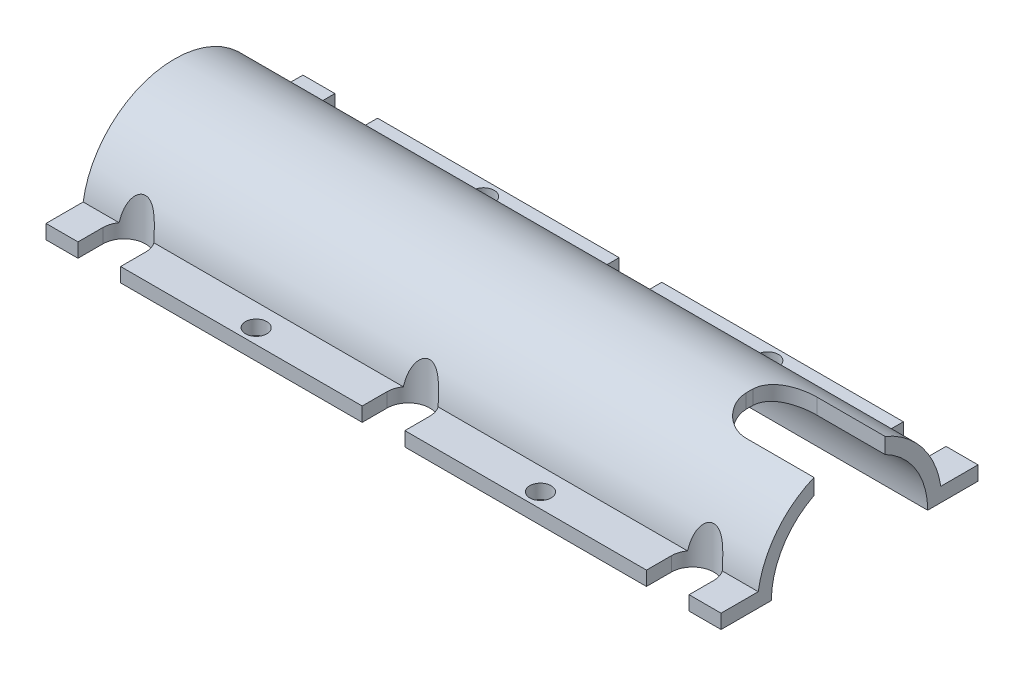
SolidWorks part; units mm, degrees
ref_plane "Спереди" through (0, 0, 0) normal (0, 0, 1) x (1, 0, 0)
ref_plane "Сверху" through (0, 0, 0) normal (0, 1, 0) x (1, 0, 0)
ref_plane "Справа" through (0, 0, 0) normal (1, 0, 0) x (0, 0, -1)
sketch "Эскиз1" plane through (0, 0, 0) normal (1, 0, 0) x (0, 0, -1)
  line L0 (11, 0) -> (18.0795, 0)
  line L1 (18.0795, 0) -> (18.0795, 2)
  line L2 (18.0795, 2) -> (12.8481, 2)
  line L3 (0, 0) -> (0, 11) construction
  line L4 (-18.0795, 2) -> (-12.848, 2.0004)
  line L5 (-18.0795, 0) -> (-18.0795, 2)
  line L6 (-11, 0) -> (-18.0795, 0)
  arc A0 (-11, 0) -> (11, 0) centre (0, 0) cw
  arc A4 (-12.848, 2.0004) -> (12.8481, 2) centre (0, 0) cw
  dimension "D1" = 2
  dimension "D2" = 13.0028
extrude "Бобышка-Вытянуть1" add sketch "Эскиз1" along normal blind 95
sketch "Эскиз2" plane through (0, 2.0015, 0.0002) normal (0, 1, 0.0001) x (1, 0, 0)
  line L0 (0, -18.0793) -> (0, -14.5793) construction
  line L1 (4.5, -14.5793) -> (4.5, -18.2988)
  line L2 (0, -12.8479) -> (0, -18.0793) construction
  line L5 (0, -14.5793) -> (7.5, -14.5793) construction
  line L6 (4.5, -18.2988) -> (10.5, -18.2988)
  line L32 (10.5, -18.2988) -> (10.5, -14.5793)
  line L33 (50.5, -18.2988) -> (50.5, -14.5793)
  line L34 (44.5, -14.5793) -> (44.5, -18.2988)
  line L35 (44.5, -18.2988) -> (50.5, -18.2988)
  line L36 (90.5, -18.2988) -> (90.5, -14.5793)
  line L37 (84.5, -14.5793) -> (84.5, -18.2988)
  line L38 (84.5, -18.2988) -> (90.5, -18.2988)
  line L39 (84.5, 18.2988) -> (90.5, 18.2988)
  line L40 (84.5, 14.5793) -> (84.5, 18.2988)
  line L41 (90.5, 18.2988) -> (90.5, 14.5793)
  line L42 (44.5, 18.2988) -> (50.5, 18.2988)
  line L43 (44.5, 14.5793) -> (44.5, 18.2988)
  line L44 (50.5, 18.2988) -> (50.5, 14.5793)
  line L45 (4.5, 18.2988) -> (10.5, 18.2988)
  line L46 (4.5, 14.5793) -> (4.5, 18.2988)
  line L47 (10.5, 18.2988) -> (10.5, 14.5793)
  circle A0 centre (27.5, -16) radius 1.5
  circle A1 centre (67.5, -16) radius 1.5
  circle A2 centre (67.5, 16) radius 1.5
  circle A3 centre (27.5, 16) radius 1.5
  arc A10 (10.5, -14.5793) -> (4.5, -14.5793) centre (7.5, -14.5793) ccw
  arc A11 (50.5, -14.5793) -> (44.5, -14.5793) centre (47.5, -14.5793) ccw
  arc A12 (90.5, -14.5793) -> (84.5, -14.5793) centre (87.5, -14.5793) ccw
  arc A13 (90.5, 14.5793) -> (84.5, 14.5793) centre (87.5, 14.5793) cw
  arc A14 (50.5, 14.5793) -> (44.5, 14.5793) centre (47.5, 14.5793) cw
  arc A15 (10.5, 14.5793) -> (4.5, 14.5793) centre (7.5, 14.5793) cw
  dimension "D1" = 2
  dimension "D2" = 3
extrude "Вырез-Вытянуть1" cut sketch "Эскиз2" against normal through all and the other way through all
sketch "Эскиз3" plane through (0, 0, 0) normal (0, -1, 0) x (1, 0, 0)
  line L0 (0, 0) -> (95, 0) construction
  line L1 (95, -11) -> (95, 11) construction
  line L3 (85.4096, 5) -> (95, 5)
  line L4 (80.9096, 0.5) -> (80.9096, -0.5)
  line L5 (85.4096, -5) -> (95, -5)
  line L6 (95, 5) -> (95, -5)
  line L7 (80.9096, 5) -> (95, -5) construction
  line L8 (80.9096, -5) -> (95, 5) construction
  arc A0 (80.9096, 0.5) -> (85.4096, 5) centre (85.4096, 0.5) cw
  arc A1 (80.9096, -0.5) -> (85.4096, -5) centre (85.4096, -0.5) ccw
  point P5 (87.9548, 0)
  dimension "D1" = 4.5
  dimension "D2" = 4.5
extrude "Вырез-Вытянуть2" cut sketch "Эскиз3" against normal through all
